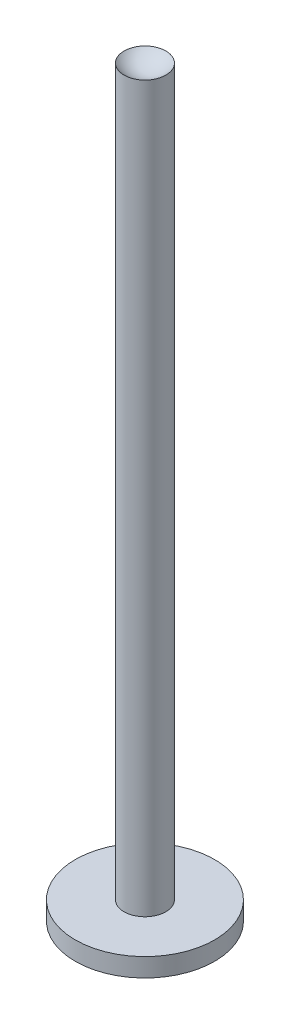
SolidWorks part; units mm, degrees
material "AISI 1020"
ref_plane "Front Plane" through (0, 0, 0) normal (0, 0, 1) x (1, 0, 0)
ref_plane "Top Plane" through (0, 0, 0) normal (0, 1, 0) x (1, 0, 0)
ref_plane "Right Plane" through (0, 0, 0) normal (1, 0, 0) x (0, 0, -1)
sketch "Sketch1" plane through (0, 0, 0) normal (0, 1, 0) x (1, 0, 0)
  circle A0 centre (0, 0) radius 75
  dimension "D1" = 150
extrude "Boss-Extrude1" add sketch "Sketch1" along normal blind 20
sketch "Sketch2" plane through (0, 20, 0) normal (0, 1, 0) x (1, 0, 0)
  circle A0 centre (0, 0) radius 22.5
  dimension "D1" = 45
extrude "Boss-Extrude2" add sketch "Sketch2" along normal blind 780
ref_plane "Plane1" through (0, 0, 22.5) normal (0, 0, 1) x (1, 0, 0)
sketch "Sketch3" plane through (0, 0, 22.5) normal (0, 0, 1) x (1, 0, 0)
  line L0 (-20, 479) -> (20, 479)
  line L1 (-20, 479) -> (-20, 370)
  line L2 (20, 479) -> (20, 370)
  line L3 (-20, 370) -> (20, 370)
  line L4 (0, 363.229) -> (0, 541.8005) construction
  point P7 (19.291, 396.2289)
  dimension "D1" = 109
  dimension "D2" = 40
  dimension "D3" = 370
sketch "Sketch4" plane through (0, 0, 0) normal (1, 0, 0) x (0, 0, -1)
  line L0 (0, 783.6975) -> (0, 804.7971) construction
  line L1 (22.5, 800) -> (-22.5, 800) construction
  line L2 (0, 800) -> (-22.5, 800)
  line L3 (0, 790) -> (8.6407, 790) construction
  line L4 (0, 790) -> (0, 800)
  arc A0 (-22.5, 800) -> (0, 790) centre (0, 820.3125) ccw
  dimension "D1" = 10
revolve "Cut-Revolve1" cut sketch "Sketch4" angle 360 about L0
ref_point "Point1"
equation "\"base_dia\"= 150'diameter of the base of the flare"
equation "\"D1@Sketch1\"=\"base_dia\""
equation "\"concave_depth\"= 10"
equation "\"D1@Sketch4\"=\"concave_depth\""
